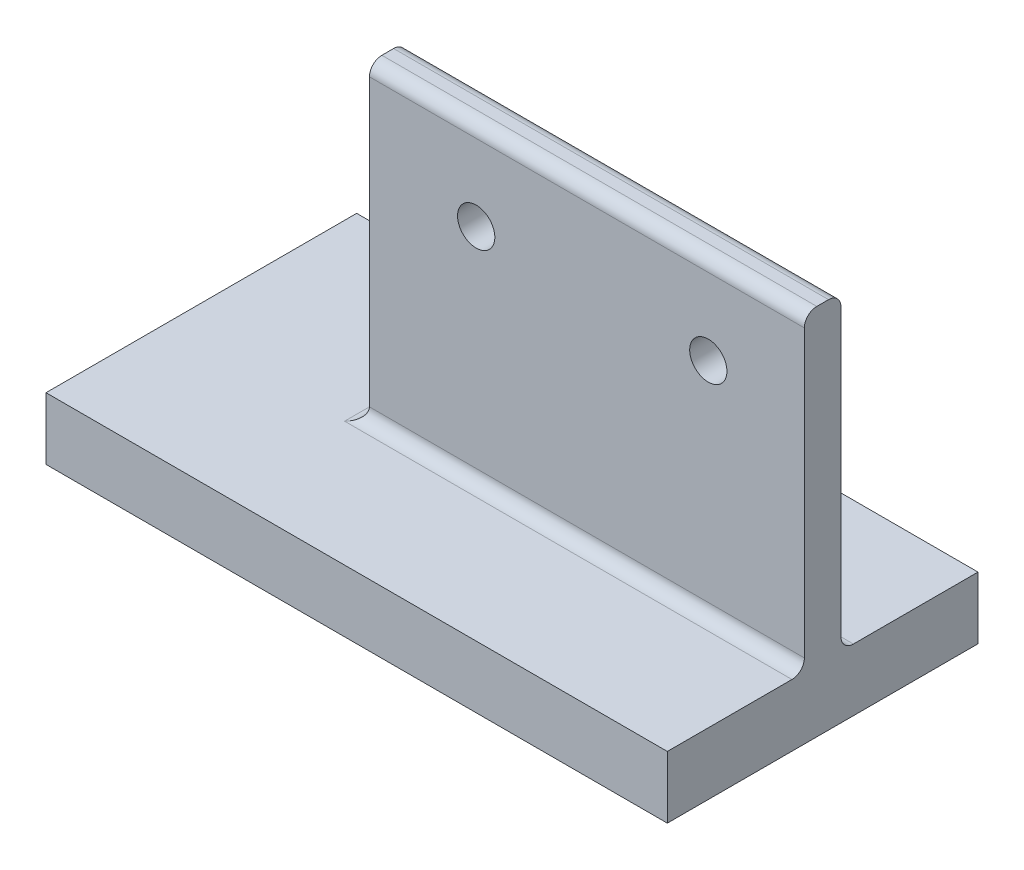
SolidWorks part; units mm, degrees
ref_plane "Front Plane" through (0, 0, 0) normal (0, 0, 1) x (1, 0, 0)
ref_plane "Top Plane" through (0, 0, 0) normal (0, 1, 0) x (1, 0, 0)
ref_plane "Right Plane" through (0, 0, 0) normal (1, 0, 0) x (0, 0, -1)
sketch "Sketch1" plane through (0, 0, 0) normal (0, 1, 0) x (1, 0, 0)
  line L1 (-43.1002, 23.2514) -> (56.8998, 23.2514)
  line L2 (-43.1002, 23.2514) -> (-43.1002, -26.7486)
  line L3 (-43.1002, -26.7486) -> (56.8998, -26.7486)
  line L4 (56.8998, 23.2514) -> (56.8998, -26.7486)
extrude "Boss-Extrude1" add sketch "Sketch1" along normal blind 10
sketch "Sketch2" plane through (0, 0, 0) normal (0, 1, 0) x (1, 0, 0)
  line L1 (56.8998, -26.7486) -> (56.8998, 23.2514) construction
  line L2 (-13.1002, 1.195) -> (56.8998, 1.195)
  line L3 (-13.1002, 1.195) -> (-13.1002, -4.6922)
  line L4 (-13.1002, -4.6922) -> (56.8998, -4.6922)
  line L5 (56.8998, 1.195) -> (56.8998, -4.6922)
  line L6 (-13.1002, 1.195) -> (56.8998, -4.6922) construction
  line L7 (-13.1002, -4.6922) -> (56.8998, 1.195) construction
  point P4 (6.8998, -1.7486)
extrude "Boss-Extrude2" add sketch "Sketch2" along normal blind 60
sketch "Sketch3" plane through (0, 0, 4.6922) normal (0, 0, 1) x (1, 0, 0)
  circle A0 centre (4.0785, 45.714) radius 3
  circle A1 centre (41.4377, 45.714) radius 3
extrude "Cut-Extrude1" cut sketch "Sketch3" against normal blind 10 and the other way blind 10
fillet "Fillet1" radius 2 1 edges at (21.8998, 60, 4.6922)
fillet "Fillet2" radius 2 1 edges at (21.8998, 60, -1.195)
ref_plane "Plane2" through (0, 0, 4.6922) normal (0, 0, 1) x (1, 0, 0)
fillet "Fillet3" radius 2 1 edges at (21.8998, 10, -1.195)
fillet "Fillet4" radius 2 1 edges at (21.8998, 10, 4.6922)
fillet "Fillet5" radius 2 1 edges at (-13.1002, 10, 1.7486)
